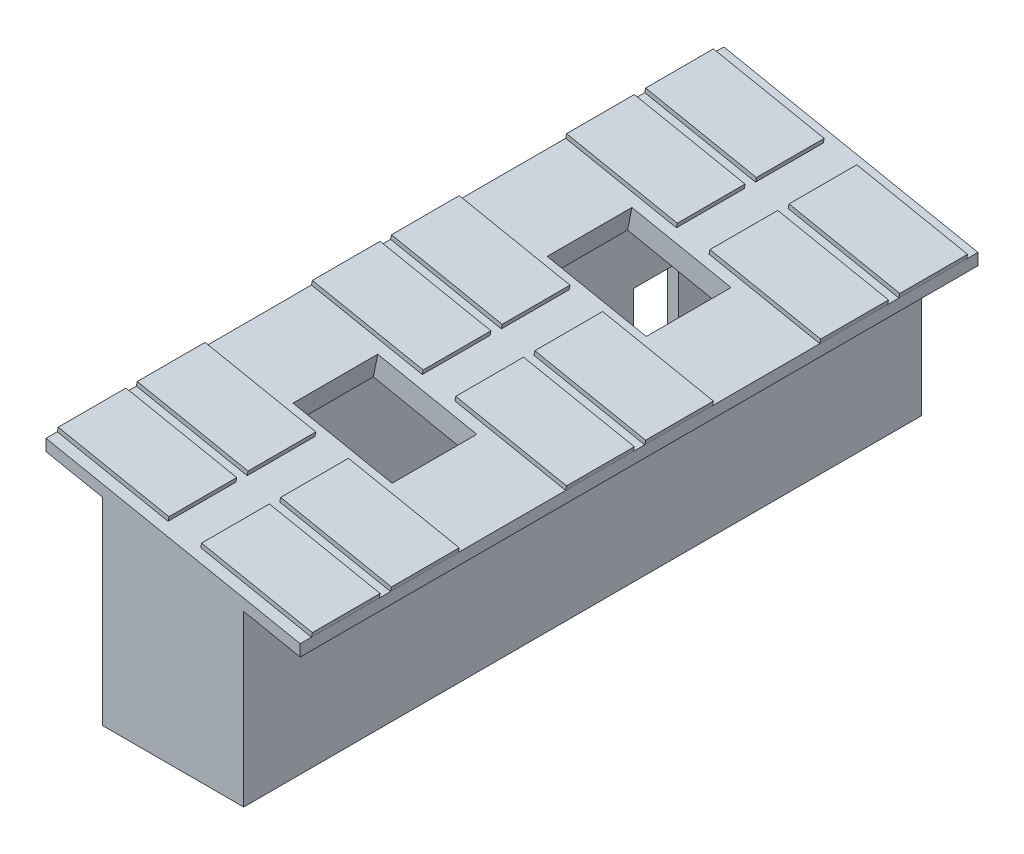
SolidWorks part; units mm, degrees
ref_plane "Front Plane" through (0, 0, 0) normal (0, 0, 1) x (1, 0, 0)
ref_plane "Top Plane" through (0, 0, 0) normal (0, 1, 0) x (1, 0, 0)
ref_plane "Right Plane" through (0, 0, 0) normal (1, 0, 0) x (0, 0, -1)
sketch "Sketch1" plane through (0, 0, 0) normal (0, 0, 1) x (1, 0, 0)
  line L0 (0, 0) -> (0, -3500)
  line L1 (0, -3500) -> (2500, -3500)
  line L2 (2500, -3500) -> (2500, -500)
  line L3 (2500, -500) -> (0, 0)
  line L4 (200, -236.3318) -> (200, -3300)
  line L5 (200, -3300) -> (2300, -3300)
  line L6 (2300, -3300) -> (2300, -663.9608)
  line L7 (2300, -663.9608) -> (200, -236.3318)
  line L8 (-1000, 200) -> (3500, -700)
  line L9 (3500, -700) -> (3500, -496.0392)
  line L10 (3500, -496.0392) -> (-1000, 403.9608)
  line L11 (-1000, 403.9608) -> (-1000, 200)
  point P11 (-1000, 301.9804)
  dimension "D1" = 3000
  dimension "D2" = 2500
  dimension "D3" = 3500
  dimension "D4" = 0.2
  dimension "D5" = 200
  dimension "D6" = 200
  dimension "D7" = 200
  dimension "D8" = 200
  dimension "D9" = 200
  dimension "D10" = 1000
  dimension "D11" = 1000
  dimension "D12" = 0
extrude "Boss-Extrude1" add sketch "Sketch1" along normal blind 12000 contours L2 L3 L0 L1 L7 L6 L5 L4 | L10 L11 L8 L3 L9
sketch "Sketch2" plane through (39.2232, 196.1161, 0) normal (0.1961, 0.9806, 0) x (0.9806, -0.1961, 0)
  line L0 (-1059.8039, -12000) -> (-1059.8039, 0) construction
  line L1 (-1059.8039, -11800) -> (940.1961, -11800)
  line L2 (-1059.8039, -11800) -> (-1059.8039, -10600)
  line L3 (-1059.8039, -10600) -> (940.1961, -10600)
  line L4 (940.1961, -11800) -> (940.1961, -10600)
  line L5 (1529.3137, -11800) -> (3529.3137, -11800)
  line L6 (1529.3137, -11800) -> (1529.3137, -10600)
  line L7 (1529.3137, -10600) -> (3529.3137, -10600)
  line L8 (3529.3137, -11800) -> (3529.3137, -10600)
  line L9 (-1059.8039, -10400) -> (940.1961, -10400)
  line L10 (-1059.8039, -10400) -> (-1059.8039, -9200)
  line L11 (-1059.8039, -9200) -> (940.1961, -9200)
  line L12 (940.1961, -10400) -> (940.1961, -9200)
  line L13 (1529.3137, -10400) -> (3529.3137, -10400)
  line L14 (1529.3137, -10400) -> (1529.3137, -9200)
  line L15 (1529.3137, -9200) -> (3529.3137, -9200)
  line L16 (3529.3137, -10400) -> (3529.3137, -9200)
  line L17 (3529.3137, -12000) -> (3529.3137, 0) construction
  line L18 (3529.3137, -12000) -> (-1059.8039, -12000) construction
  line L19 (3529.3137, 0) -> (-1059.8039, 0) construction
  line L20 (-1059.8039, -7300) -> (940.1961, -7300)
  line L21 (-1059.8039, -7300) -> (-1059.8039, -6100)
  line L22 (-1059.8039, -6100) -> (940.1961, -6100)
  line L23 (940.1961, -7300) -> (940.1961, -6100)
  line L24 (3529.3137, -7300) -> (1529.3137, -7300)
  line L25 (3529.3137, -7300) -> (3529.3137, -6100)
  line L26 (3529.3137, -6100) -> (1529.3137, -6100)
  line L27 (1529.3137, -7300) -> (1529.3137, -6100)
  line L28 (-1059.8039, -200) -> (940.1961, -200)
  line L29 (-1059.8039, -200) -> (-1059.8039, -1400)
  line L30 (-1059.8039, -1400) -> (940.1961, -1400)
  line L31 (940.1961, -200) -> (940.1961, -1400)
  line L32 (3529.3137, -200) -> (1529.3137, -200)
  line L33 (3529.3137, -200) -> (3529.3137, -1400)
  line L34 (3529.3137, -1400) -> (1529.3137, -1400)
  line L35 (1529.3137, -200) -> (1529.3137, -1400)
  line L36 (-1059.8039, -1600) -> (940.1961, -1600)
  line L37 (-1059.8039, -1600) -> (-1059.8039, -2800)
  line L38 (-1059.8039, -2800) -> (940.1961, -2800)
  line L39 (940.1961, -1600) -> (940.1961, -2800)
  line L40 (-1059.8039, -4700) -> (940.1961, -4700)
  line L41 (-1059.8039, -4700) -> (-1059.8039, -5900)
  line L42 (-1059.8039, -5900) -> (940.1961, -5900)
  line L43 (940.1961, -4700) -> (940.1961, -5900)
  line L44 (3529.3137, -1600) -> (1529.3137, -1600)
  line L45 (3529.3137, -1600) -> (3529.3137, -2800)
  line L46 (3529.3137, -2800) -> (1529.3137, -2800)
  line L47 (1529.3137, -1600) -> (1529.3137, -2800)
  line L48 (3529.3137, -4700) -> (1529.3137, -4700)
  line L49 (3529.3137, -4700) -> (3529.3137, -5900)
  line L50 (3529.3137, -5900) -> (1529.3137, -5900)
  line L51 (1529.3137, -4700) -> (1529.3137, -5900)
  dimension "D1" = 0
  dimension "D2" = 0
  dimension "D3" = 0
  dimension "D4" = 0
  dimension "D5" = 0
  dimension "D6" = 2000
  dimension "D7" = 2000
  dimension "D8" = 2000
  dimension "D9" = 200
  dimension "D10" = 200
  dimension "D11" = 200
  dimension "D12" = 200
  dimension "D13" = 1200
  dimension "D14" = 1200
  dimension "D15" = 1200
  dimension "D16" = 1200
  dimension "D17" = 200
  dimension "D18" = 200
  dimension "D19" = 1200
  dimension "D20" = 1200
  dimension "D21" = 200
  dimension "D22" = 1200
  dimension "D23" = 200
  dimension "D24" = 1200
  dimension "D25" = 1200
  dimension "D26" = 1200
  dimension "D27" = 1200
  dimension "D28" = 1200
  dimension "D29" = 200
  dimension "D30" = 200
  dimension "D31" = 0
  dimension "D32" = 1900
extrude "Boss-Extrude2" add sketch "Sketch2" along normal blind 80
sketch "Sketch3" plane through (39.2232, 196.1161, 0) normal (0.1961, 0.9806, 0) x (0.9806, -0.1961, 0)
  line L0 (-1059.8039, -2800) -> (940.1961, -2800) construction
  line L1 (340.1961, -7500) -> (2129.3137, -7500)
  line L2 (340.1961, -7500) -> (340.1961, -9000)
  line L3 (340.1961, -9000) -> (2129.3137, -9000)
  line L4 (2129.3137, -7500) -> (2129.3137, -9000)
  line L5 (340.1961, -3000) -> (2129.3137, -3000)
  line L6 (340.1961, -3000) -> (340.1961, -4500)
  line L7 (340.1961, -4500) -> (2129.3137, -4500)
  line L8 (2129.3137, -3000) -> (2129.3137, -4500)
  line L9 (940.1961, -4700) -> (-1059.8039, -4700) construction
  line L10 (-1059.8039, -7300) -> (940.1961, -7300) construction
  line L11 (940.1961, -9200) -> (-1059.8039, -9200) construction
  line L12 (-1059.8039, -9200) -> (-1059.8039, -7300) construction
  line L13 (3529.3137, -9200) -> (3529.3137, -7300) construction
  line L14 (-1059.8039, -4700) -> (-1059.8039, -2800) construction
  line L15 (3529.3137, -4700) -> (3529.3137, -2800) construction
  dimension "D1" = 200
  dimension "D2" = 200
  dimension "D3" = 200
  dimension "D4" = 200
  dimension "D5" = 1400
  dimension "D6" = 1400
  dimension "D7" = 1400
  dimension "D8" = 1400
extrude "Cut-Extrude1" cut sketch "Sketch3" against normal blind 400
sketch "Sketch4" plane through (0, 0, 12000) normal (0, 0, 1) x (1, 0, 0)
  line L8 (2500, -3500) -> (2500, -500)
  line L9 (2500, -500) -> (3500, -700)
  line L10 (3500, -700) -> (3500, -496.0392)
  line L11 (3500, -496.0392) -> (-1000, 403.9608)
  line L12 (-1000, 403.9608) -> (-1000, 200)
  line L13 (-1000, 200) -> (0, 0)
  line L14 (0, 0) -> (0, -3500)
  line L15 (0, -3500) -> (2500, -3500)
  line L16 (2500, -3500) -> (2500, -500)
  line L17 (2500, -500) -> (3500, -700)
  line L18 (3500, -700) -> (3500, -496.0392)
  line L19 (3500, -496.0392) -> (-1000, 403.9608)
  line L20 (-1000, 403.9608) -> (-1000, 200)
  line L21 (-1000, 200) -> (0, 0)
  line L22 (0, 0) -> (0, -3500)
  line L23 (0, -3500) -> (2500, -3500)
  dimension "D1" = 0
extrude "Boss-Extrude3" add sketch "Sketch4" against normal blind 200
sketch "Sketch5" plane through (0, 0, 0) normal (0, 0, -1) x (-1, 0, 0)
  line L8 (-2500, -500) -> (-2500, -3500)
  line L9 (-2500, -3500) -> (0, -3500)
  line L10 (0, -3500) -> (0, 0)
  line L11 (0, 0) -> (1000, 200)
  line L12 (1000, 200) -> (1000, 403.9608)
  line L13 (1000, 403.9608) -> (-3500, -496.0392)
  line L14 (-3500, -496.0392) -> (-3500, -700)
  line L15 (-3500, -700) -> (-2500, -500)
  line L16 (-2500, -500) -> (-2500, -3500)
  line L17 (-2500, -3500) -> (0, -3500)
  line L18 (0, -3500) -> (0, 0)
  line L19 (0, 0) -> (1000, 200)
  line L20 (1000, 200) -> (1000, 403.9608)
  line L21 (1000, 403.9608) -> (-3500, -496.0392)
  line L22 (-3500, -496.0392) -> (-3500, -700)
  line L23 (-3500, -700) -> (-2500, -500)
  dimension "D1" = 0
extrude "Boss-Extrude4" add sketch "Sketch5" against normal blind 200
sketch "Sketch6" plane through (0, 0, 0) normal (-1, 0, 0) x (0, 0, 1)
  line L0 (11800, -3300) -> (200, -3300) construction
  line L1 (2000, -3300) -> (2800, -3300)
  line L2 (2000, -3300) -> (2000, -1300)
  line L3 (2000, -1300) -> (2800, -1300)
  line L4 (2800, -3300) -> (2800, -1300)
  line L5 (0, 0) -> (0, -3500) construction
  line L6 (9200, -3300) -> (10000, -3300)
  line L7 (9200, -3300) -> (9200, -1300)
  line L8 (9200, -1300) -> (10000, -1300)
  line L9 (10000, -3300) -> (10000, -1300)
  line L10 (12000, 0) -> (12000, -3500) construction
  dimension "D1" = 2000
  dimension "D2" = 2800
  dimension "D3" = 2000
  dimension "D4" = 2800
  dimension "D5" = 2000
  dimension "D6" = 2000
extrude "Cut-Extrude2" cut sketch "Sketch6" against normal blind 200
sketch "Sketch7" plane through (2300, 0, 0) normal (-1, 0, 0) x (0, 0, 1)
  line L0 (200, -236.3318) -> (200, -3300) construction
  line L1 (200, -2580) -> (11800, -2580)
  line L2 (200, -2580) -> (200, -2640)
  line L3 (200, -2640) -> (11800, -2640)
  line L4 (11800, -2580) -> (11800, -2640)
  line L5 (11800, -236.3318) -> (11800, -3300) construction
  line L6 (2000, -3300) -> (200, -3300) construction
  dimension "D1" = 60
  dimension "D2" = 720
extrude "Boss-Extrude5" add sketch "Sketch7" along normal blind 800
sketch "Sketch8" plane through (0, 0, 11800) normal (0, 0, -1) x (-1, 0, 0)
  line L0 (-2300, -2580) -> (-2300, -663.9608) construction
  circle A0 centre (-2180, -763.9608) radius 100
  circle A1 centre (-2180, -763.9608) radius 70
  dimension "D1" = 200
  dimension "D2" = 140
  dimension "D3" = 100
  dimension "D4" = 120
extrude "Boss-Extrude7" add sketch "Sketch8" along normal blind 11721
sketch "Sketch9" plane through (2300, 0, 0) normal (-1, 0, 0) x (0, 0, 1)
  line L0 (200, -2580) -> (200, -663.9608) construction
  line L1 (200, -1180) -> (11800, -1180)
  line L2 (200, -1180) -> (200, -2180)
  line L3 (200, -2180) -> (11800, -2180)
  line L4 (11800, -1180) -> (11800, -2180)
  line L5 (11800, -2580) -> (11800, -663.9608) construction
  line L6 (11800, -2580) -> (200, -2580) construction
  dimension "D1" = 1000
  dimension "D2" = 400
extrude "Boss-Extrude8" add sketch "Sketch9" along normal blind 20
